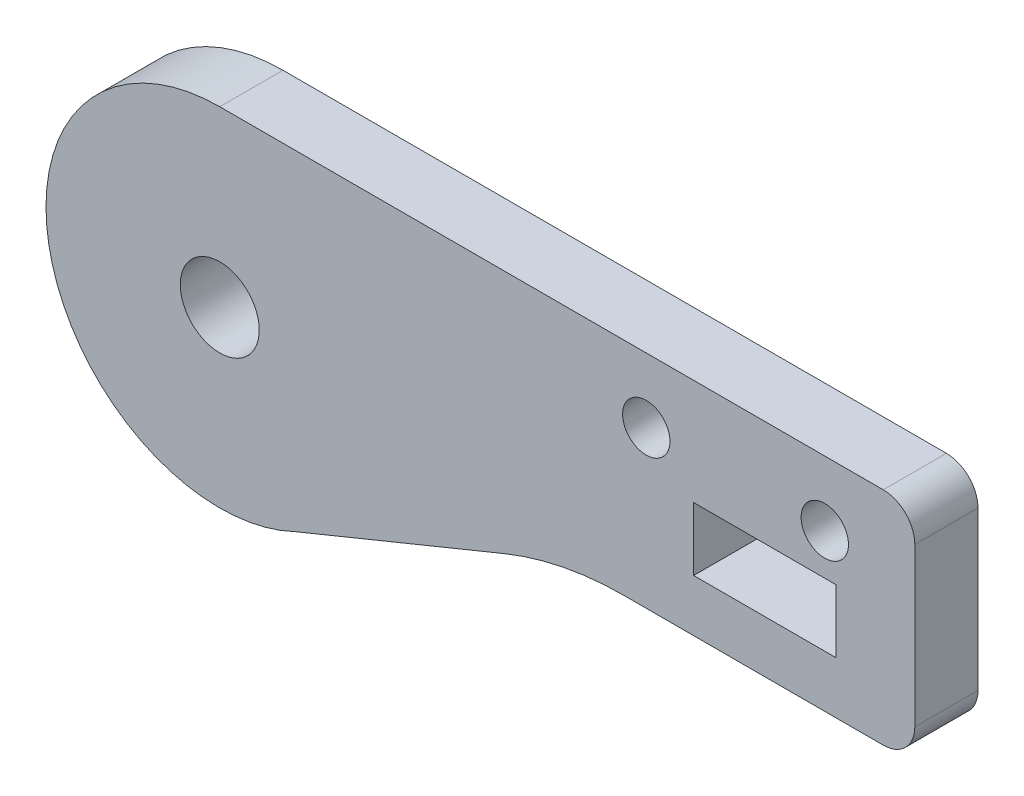
SolidWorks part; units mm, degrees
material "Beech"
ref_plane "Front Plane" through (0, 0, 0) normal (0, 0, 1) x (1, 0, 0)
ref_plane "Top Plane" through (0, 0, 0) normal (0, 1, 0) x (1, 0, 0)
ref_plane "Right Plane" through (0, 0, 0) normal (1, 0, 0) x (0, 0, -1)
sketch "Sketch1" plane through (0, 0, 0) normal (0, 0, 1) x (1, 0, 0)
  line L8 (55, 39.0986) -> (55, 29.0986)
  line L9 (53, 27.0986) -> (36.5989, 27.0986)
  line L10 (53, 41.0986) -> (11, 41.0986)
  line L11 (29.0265, 25.6096) -> (15.7722, 20.1877)
  line L12 (50, 30.3986) -> (41, 30.3986)
  line L13 (41, 30.3986) -> (41, 34.3986)
  line L14 (41, 34.3986) -> (50, 34.3986)
  line L15 (50, 30.3986) -> (50, 34.3986)
  arc A9 (36.5989, 27.0986) -> (29.0265, 25.6096) centre (36.5989, 7.0986) ccw
  arc A10 (11, 41.0986) -> (15.7722, 20.1877) centre (11, 30.0986) ccw
  circle A11 centre (38, 36.9986) radius 1.5
  circle A12 centre (49.3, 36.9986) radius 1.5
  circle A13 centre (11, 30.0986) radius 2.5
  arc A14 (53, 27.0986) -> (55, 29.0986) centre (53, 29.0986) ccw
  arc A15 (55, 39.0986) -> (53, 41.0986) centre (53, 39.0986) ccw
extrude "Boss-Extrude1" add sketch "Sketch1" along normal blind 4
